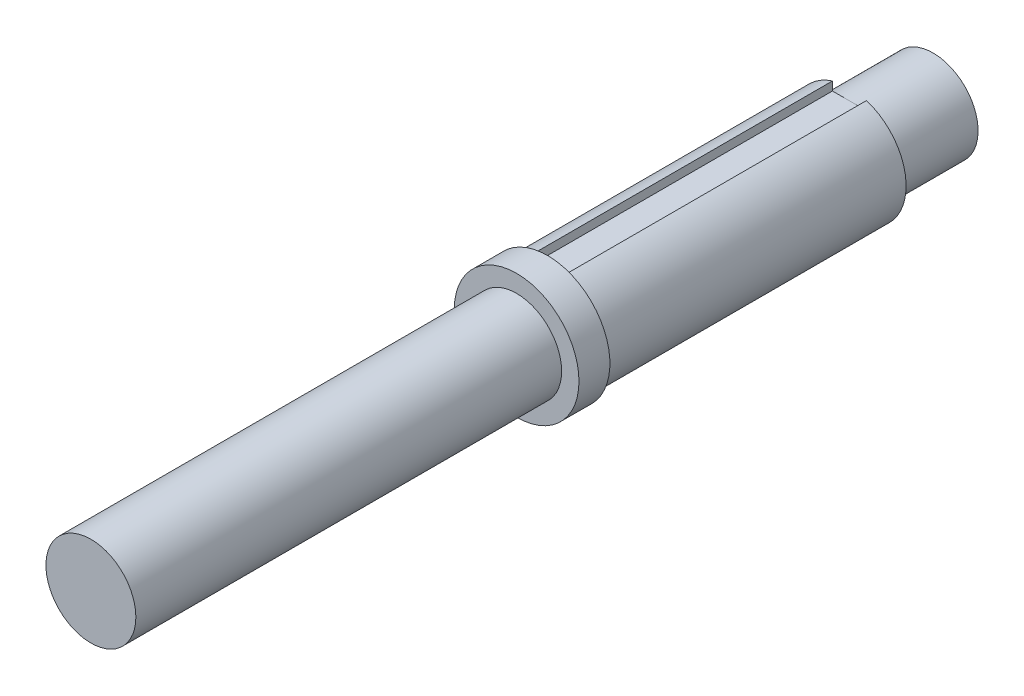
SolidWorks part; units mm, degrees
material "AISI 304"
ref_plane "Front Plane" through (0, 0, 0) normal (0, 0, 1) x (1, 0, 0)
ref_plane "Top Plane" through (0, 0, 0) normal (0, 1, 0) x (1, 0, 0)
ref_plane "Right Plane" through (0, 0, 0) normal (1, 0, 0) x (0, 0, -1)
sketch "Sketch1" plane through (0, 0, 0) normal (0, 0, 1) x (1, 0, 0)
  circle A0 centre (0, 0) radius 5.5
  dimension "D1" = 11
extrude "Boss-Extrude1" add sketch "Sketch1" along normal blind 160.3
sketch "Sketch2" plane through (0, 0, 0) normal (0, 1, 0) x (1, 0, 0)
  line L0 (0, 0) -> (0, 5.2173) construction
sketch "Sketch3" plane through (0, 0, 0) normal (0, 0, -1) x (-1, 0, 0)
  circle A0 centre (0, 0) radius 5
  dimension "D1" = 10
extrude "Cut-Extrude2" cut sketch "Sketch3" against normal blind 120 flip side to cut
sketch "Sketch4" plane through (0, 0, 160.3) normal (0, 0, 1) x (1, 0, 0)
  circle A0 centre (0, 0) radius 3.9688
  dimension "D1" = 7.9375
extrude "Cut-Extrude3" cut sketch "Sketch4" against normal blind 37.57 flip side to cut
sketch "Sketch5" plane through (0, 0, 0) normal (0, 0, -1) x (-1, 0, 0)
  circle A0 centre (0, 0) radius 3.97
  dimension "D1" = 7.94
extrude "Cut-Extrude4" cut sketch "Sketch5" against normal blind 93.36 flip side to cut
ref_plane "Plane1" through (0, 5, 0) normal (0, 1, 0) x (1, 0, 0)
sketch "Sketch9" plane through (0, 5, 0) normal (0, 1, 0) x (1, 0, 0)
  line L0 (0, -120) -> (0, -84.3327) construction
  line L1 (1.5, -120) -> (1.5, -93)
  line L2 (1.5, -93) -> (-1.5, -93)
  line L3 (-1.5, -93) -> (-1.5, -120)
  line L4 (1.5, -120) -> (-1.5, -120)
  line L6 (5, -120) -> (-5, -120) construction
  point P6 (0, -93)
  dimension "D1" = 3
  dimension "D2" = 27
extrude "Cut-Extrude6" cut sketch "Sketch9" against normal blind 1
ref_plane "Plane2" through (0, -5, 0) normal (0, -1, 0) x (-1, 0, 0)
sketch "Sketch11" plane through (0, -5, 0) normal (0, -1, 0) x (-1, 0, 0)
  line L0 (1.8837, -120.0203) -> (-1.8837, -120.0203)
  line L1 (-1.8837, -120.0203) -> (-1.8837, -93.0203)
  line L2 (-1.8837, -93.0203) -> (1.8837, -93.0203)
  line L3 (1.8837, -93.0203) -> (1.8837, -120.0203)
  line L4 (0, -120.0203) -> (0, -86.994) construction
  point P7 (0, -93.0203)
  point P8 (0, -120.0203)
  dimension "D1" = 27
extrude "Cut-Extrude7" cut sketch "Sketch11" against normal blind 1
sketch "Sketch12" plane through (0, 0, 0) normal (0, 0, -1) x (-1, 0, 0)
  circle A0 centre (0, 0) radius 15.9147
extrude "Cut-Extrude8" cut sketch "Sketch12" against normal blind 85.98
